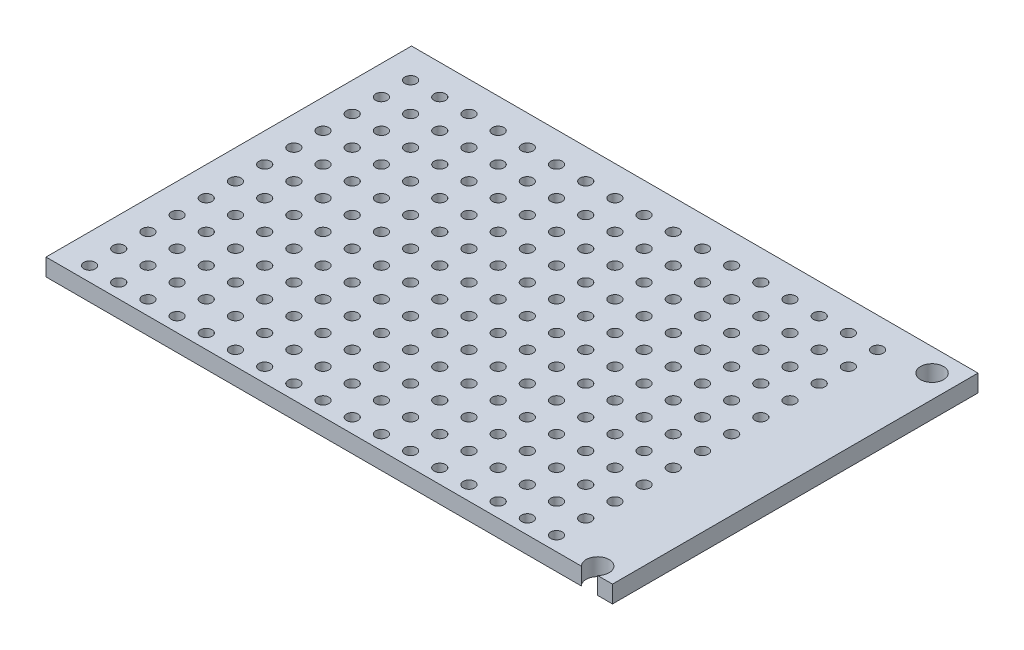
SolidWorks part; units mm, degrees
ref_plane "Front Plane" through (0, 0, 0) normal (0, 0, 1) x (1, 0, 0)
ref_plane "Top Plane" through (0, 0, 0) normal (0, 1, 0) x (1, 0, 0)
ref_plane "Right Plane" through (0, 0, 0) normal (1, 0, 0) x (0, 0, -1)
sketch "Sketch1" plane through (0, 0, 0) normal (0, 1, 0) x (1, 0, 0)
  line L1 (-22.5, -16.55) -> (22.5, -16.55)
  line L2 (-22.5, -16.55) -> (-22.5, 16.55)
  line L3 (-22.5, 16.55) -> (22.5, 16.55)
  line L4 (22.5, -16.55) -> (22.5, 16.55)
  line L5 (-22.5, -16.55) -> (22.5, 16.55) construction
  line L6 (-22.5, 16.55) -> (22.5, -16.55) construction
  point P0 (0, 0)
  dimension "D1" = 45
  dimension "D2" = 33.1
extrude "Boss-Extrude1" add sketch "Sketch1" along normal mid plane 1.5 contours L2 L3 L4 L1
sketch "Sketch2" plane through (0, 0.75, 0) normal (0, 1, 0) x (1, 0, 0)
  line L0 (-22.5, -16.55) -> (22.5, -16.55) construction
  line L1 (-22.5, -16.55) -> (-22.5, 16.55) construction
  circle A0 centre (-19.96, -14.01) radius 0.5
  dimension "D1" = 1
  dimension "D2" = 2.54
  dimension "D3" = 2.54
extrude "Cut-Extrude1" cut sketch "Sketch2" against normal through all
pattern_linear "LPattern1" count 17 spacing 2.54 along (1, 0, 0) count 12 spacing 2.54 along (0, 0, -1) of "Cut-Extrude1"
sketch "Sketch3" plane through (22.5, 0, 0) normal (1, 0, 0) x (0, 0, -1)
  line L4 (-16.55, -0.75) -> (16.55, -0.75)
  line L5 (16.55, -0.75) -> (16.55, 0.75)
  line L6 (16.55, 0.75) -> (-16.55, 0.75)
  line L7 (-16.55, 0.75) -> (-16.55, -0.75)
  line L8 (-16.55, -0.75) -> (16.55, -0.75)
  line L9 (16.55, -0.75) -> (16.55, 0.75)
  line L10 (16.55, 0.75) -> (-16.55, 0.75)
  line L11 (-16.55, 0.75) -> (-16.55, -0.75)
  dimension "D1" = 0
extrude "Boss-Extrude2" add sketch "Sketch3" along normal blind 4.3
sketch "Sketch4" plane through (0, 0.75, 0) normal (0, 1, 0) x (1, 0, 0)
  line L0 (-22.5, -16.55) -> (26.8, -16.55) construction
  line L1 (26.8, 16.55) -> (26.8, -16.55) construction
  line L2 (-22.5, 16.55) -> (26.8, 16.55) construction
  circle A0 centre (24.8, -14.55) radius 1
  circle A1 centre (24.8, 14.55) radius 1
  point P4 (0, 0)
  dimension "D1" = 2
  dimension "D2" = 2
  dimension "D3" = 2
  dimension "D4" = 2
extrude "Cut-Extrude2" cut sketch "Sketch4" against normal through all
sketch "Sketch5" plane through (0, 0, 16.55) normal (0, 0, 1) x (1, 0, 0)
  line L4 (-22.5, -0.75) -> (26.8, -0.75)
  line L5 (26.8, -0.75) -> (26.8, 0.75)
  line L6 (26.8, 0.75) -> (-22.5, 0.75)
  line L7 (-22.5, 0.75) -> (-22.5, -0.75)
  line L8 (-22.5, -0.75) -> (26.8, -0.75)
  line L9 (26.8, -0.75) -> (26.8, 0.75)
  line L10 (26.8, 0.75) -> (-22.5, 0.75)
  line L11 (-22.5, 0.75) -> (-22.5, -0.75)
  dimension "D1" = 0
extrude "Cut-Extrude3" cut sketch "Sketch5" against normal blind 1.29
